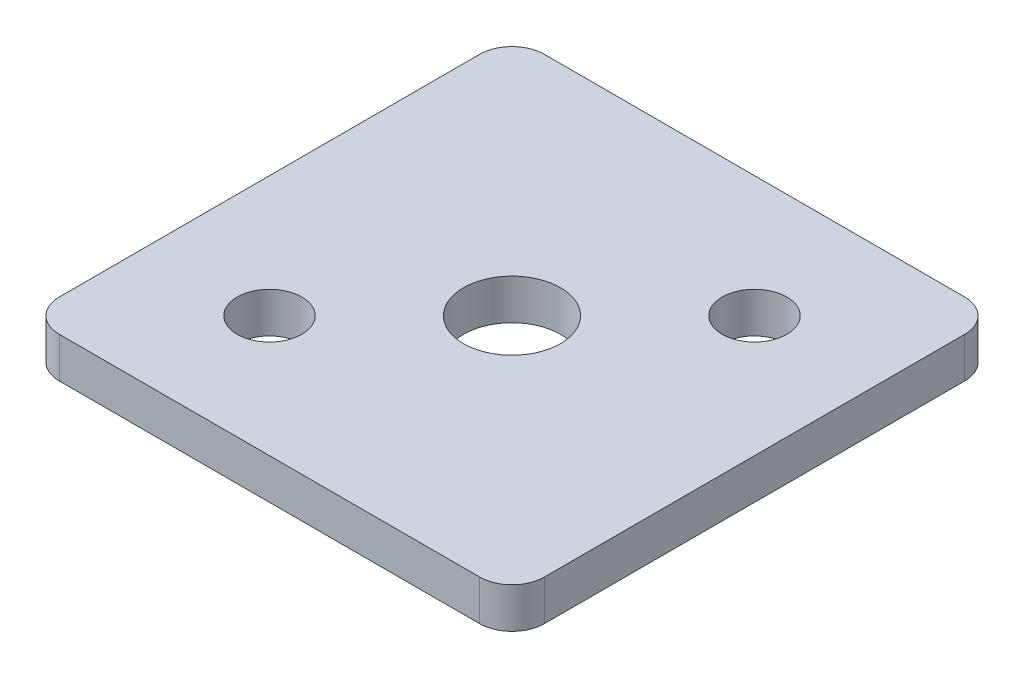
SolidWorks part; units mm, degrees
ref_plane "Front" through (0, 0, 0) normal (0, 0, 1) x (1, 0, 0)
ref_plane "Top" through (0, 0, 0) normal (0, 1, 0) x (1, 0, 0)
ref_plane "Right" through (0, 0, 0) normal (1, 0, 0) x (0, 0, -1)
sketch "Sketch1" plane through (0, 0, 0) normal (0, 1, 0) x (1, 0, 0)
  line L1 (-19.05, 19.05) -> (19.05, 19.05)
  line L2 (-19.05, 19.05) -> (-19.05, -19.05)
  line L3 (-19.05, -19.05) -> (19.05, -19.05)
  line L4 (19.05, 19.05) -> (19.05, -19.05)
  line L5 (-9.525, 9.525) -> (9.525, 9.525) construction
  line L6 (-9.525, 9.525) -> (-9.525, -9.525) construction
  line L7 (-9.525, -9.525) -> (9.525, -9.525) construction
  line L8 (9.525, 9.525) -> (9.525, -9.525) construction
  circle A0 centre (9.525, 9.525) radius 2.54
  circle A1 centre (-9.525, -9.525) radius 2.54
  circle A2 centre (0, 0) radius 3.81
  point P4 (0, 19.05)
  point P6 (-19.05, 0)
  point P11 (0, 9.525)
  point P12 (-9.525, 0)
  dimension "D5" = 5.08
  dimension "D6" = 7.62
  dimension "D1" = 38.1
  dimension "D2" = 38.1
  dimension "D3" = 19.05
  dimension "D4" = 19.05
extrude "Boss-Extrude1" add sketch "Sketch1" along normal blind 3.175
fillet "Fillet1" radius 2.54 4 edges at (-19.05, 1.5875, -19.05) (19.05, 1.5875, -19.05) (19.05, 1.5875, 19.05) (-19.05, 1.5875, 19.05)
